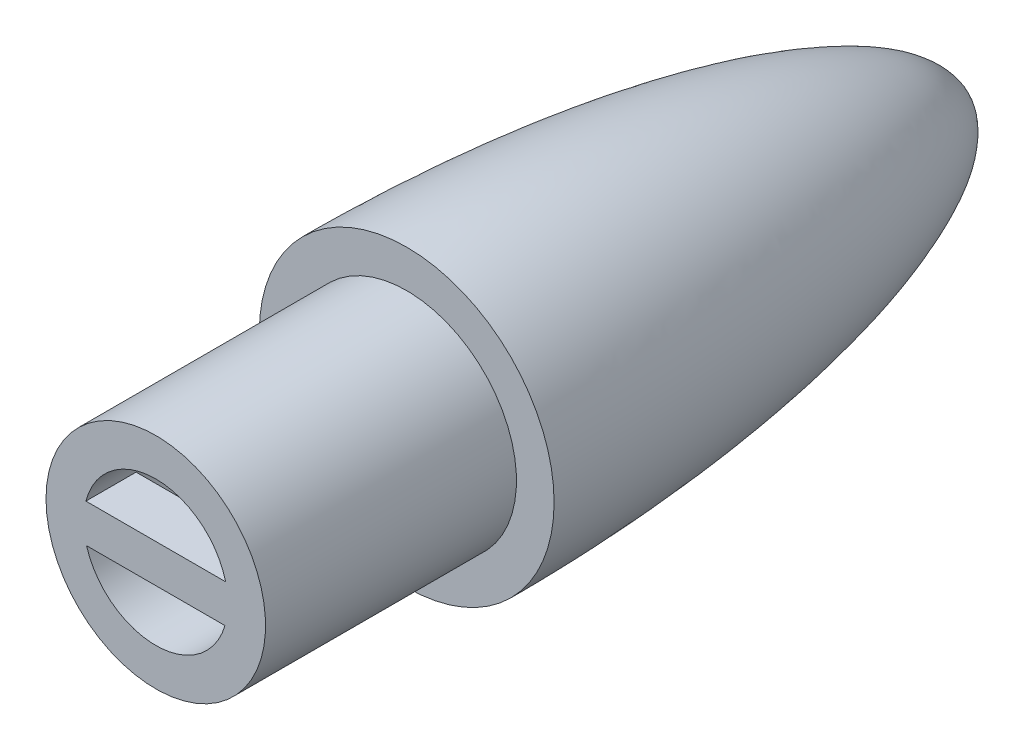
SolidWorks part; units mm, degrees
ref_plane "Front Plane" through (0, 0, 0) normal (0, 0, 1) x (1, 0, 0)
ref_plane "Top Plane" through (0, 0, 0) normal (0, 1, 0) x (1, 0, 0)
ref_plane "Right Plane" through (0, 0, 0) normal (1, 0, 0) x (0, 0, -1)
sketch "Sketch1" plane through (0, 0, 0) normal (0, 1, 0) x (1, 0, 0)
  line L0 (0, 11.4224) -> (0, 8.9224)
  line L4 (-11.75, -32.5776) -> (-8.75, -32.5776)
  line L5 (-8.75, -32.5776) -> (-8.75, -52.5776)
  line L6 (-8.75, -52.5776) -> (-5.75, -52.5776)
  line L7 (-5.75, -52.5776) -> (-5.75, -29.5776)
  line L8 (-5.75, -29.5776) -> (-8.75, -29.5776)
  line L12 (0, 8.9224) -> (-6.0343, -1.9436)
  line L13 (-6.0343, -1.9436) -> (-8.75, -29.5776)
  spline S0 degree 3 poles (0, 11.4224) (-1.2784, 11.417) (-3.8731, 9.5587) (-5.9448, 5.6272) (-7.7109, 0.9059) (-8.8856, -3.5703) (-9.8914, -8.5946) (-10.6705, -13.7918) (-11.219, -19.122) (-11.5302, -23.7907) (-11.7075, -28.0933) (-11.75, -30.9224) (-11.75, -32.5776) knots 0 0 0 0 0.077096 0.191083 0.276022 0.396034 0.482753 0.599803 0.727919 0.821235 0.895417 1 1 1 1
  dimension "D2" = 8.75
  dimension "D1" = 2.5
  dimension "D3" = 44
  dimension "D5" = 3
  dimension "D6" = 20
  dimension "D7" = 3
  dimension "D8" = 23
revolve "Revolve1" add sketch "Sketch1" angle 360 about L0
sketch "Sketch3" plane through (0, 0, 52.5776) normal (0, 0, 1) x (1, 0, 0)
  line L1 (-6.5367, 1.4299) -> (6.631, 1.4299)
  line L2 (-6.5367, 1.4299) -> (-6.5367, -1.6185)
  line L3 (-6.5367, -1.6185) -> (6.631, -1.6185)
  line L4 (6.631, 1.4299) -> (6.631, -1.6185)
extrude "Boss-Extrude7" add sketch "Sketch3" against normal blind 4
